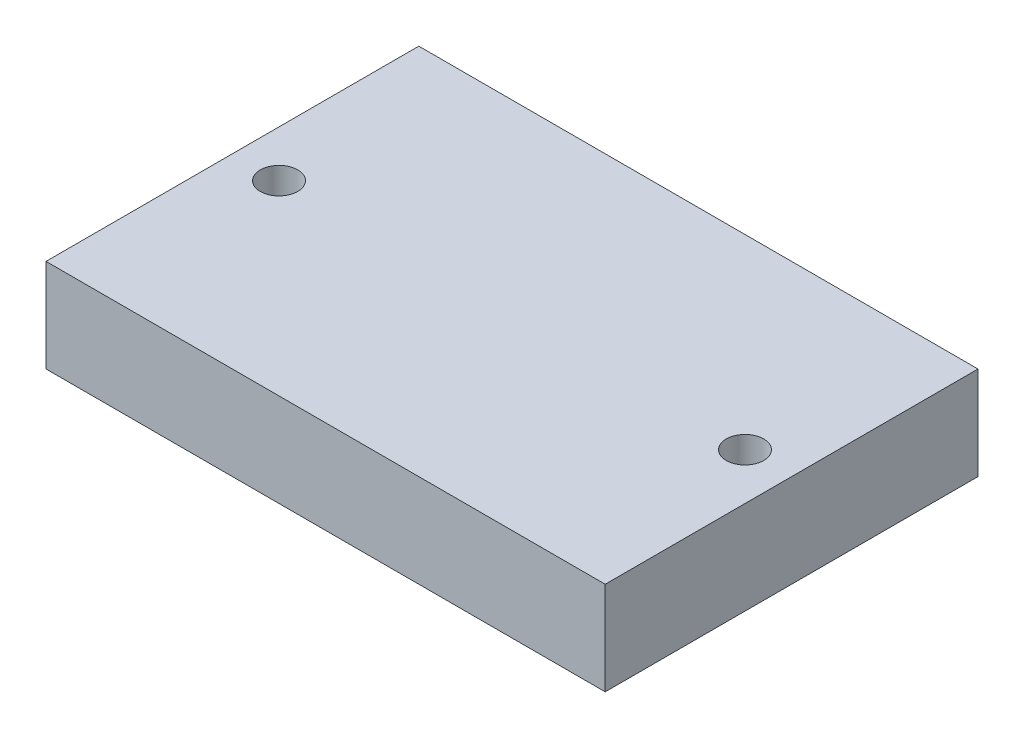
SolidWorks part; units mm, degrees
ref_plane "Front Plane" through (0, 0, 0) normal (0, 0, 1) x (1, 0, 0)
ref_plane "Top Plane" through (0, 0, 0) normal (0, 1, 0) x (1, 0, 0)
ref_plane "Right Plane" through (0, 0, 0) normal (1, 0, 0) x (0, 0, -1)
sketch "Sketch1" plane through (0, 0, 0) normal (0, 1, 0) x (1, 0, 0)
  line L1 (-38.1, -25.4) -> (38.1, -25.4)
  line L2 (-38.1, -25.4) -> (-38.1, 25.4)
  line L3 (-38.1, 25.4) -> (38.1, 25.4)
  line L4 (38.1, -25.4) -> (38.1, 25.4)
  line L5 (-38.1, -25.4) -> (38.1, 25.4) construction
  line L6 (-38.1, 25.4) -> (38.1, -25.4) construction
  point P0 (0, 0)
  dimension "D1" = 50.8
  dimension "D2" = 76.2
extrude "Boss-Extrude1" add sketch "Sketch1" along normal blind 12.7 contours L3 L4 L1 L2
ref_plane "Plane1" through (0, 0, 0) normal (-1, 0, 0) x (0, 0, 1)
ref_plane "Plane2" through (0, 0, 0) normal (0, 0, -1) x (-1, 0, 0)
hole_wizard "1/4-20 Tapped Hole1" positions "Sketch4" profile "Sketch5" tap size "1/4-20" standard "ANSI Inch" end condition through all
sketch "Sketch4" plane through (0, 12.7, 0) normal (0, 1, 0) x (1, 0, 0)
  line L0 (0, 6.985) -> (0, -6.985) construction
  point P0 (-31.75, 0)
  point P5 (31.75, 0)
  dimension "D1" = 31.75
sketch "Sketch5" plane through (-31.75, 12.7, 0) normal (1, 0, 0) x (0, 0, 1)
  line L0 (0, 0) -> (0, 12.7)
  line L1 (0, 12.7) -> (2.5527, 12.7)
  line L2 (2.5527, 12.7) -> (2.5527, 0)
  line L5 (2.5527, 0) -> (0, 0)
  line L11 (0, -6.35) -> (0, 107.95) construction
  dimension "Thru Tap Drill Dia." = 5.1054
  dimension "Thru Tap Drill Depth" = 12.7
cosmetic thread "Hole Thread1" parameters "D2"=6.35
cosmetic thread "Hole Thread2" parameters "D2"=6.35
